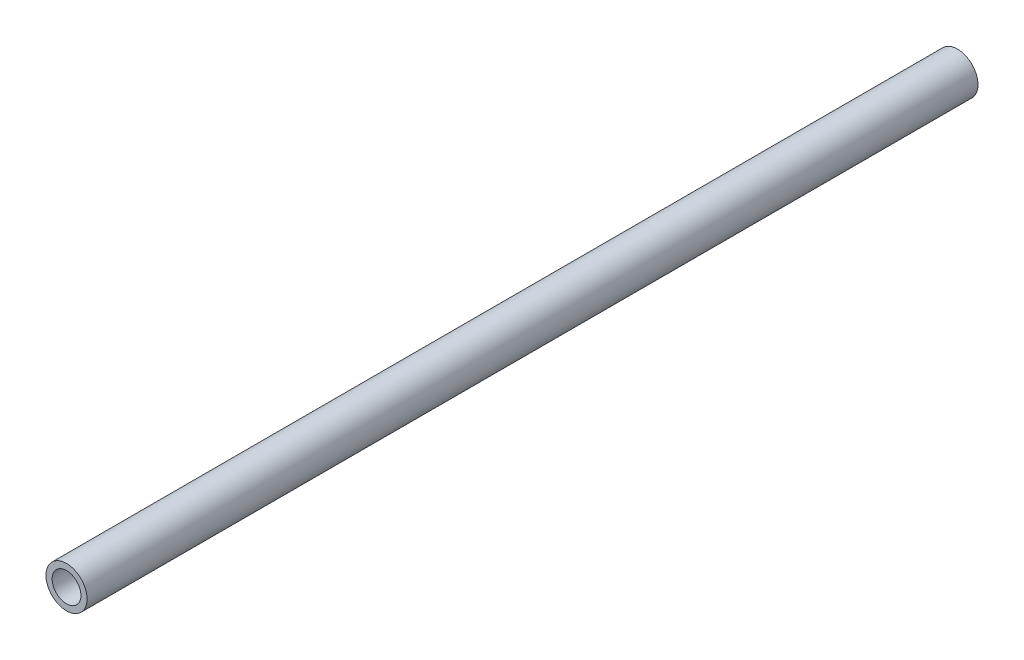
SolidWorks part; units mm, degrees
material "6063-T5"
ref_plane "Front Plane" through (0, 0, 0) normal (0, 0, 1) x (1, 0, 0)
ref_plane "Top Plane" through (0, 0, 0) normal (0, 1, 0) x (1, 0, 0)
ref_plane "Right Plane" through (0, 0, 0) normal (1, 0, 0) x (0, 0, -1)
sketch "Sketch1" plane through (0, 0, 0) normal (0, 0, 1) x (1, 0, 0)
  circle A0 centre (0, 0) radius 3.345
  circle A1 centre (0, 0) radius 2.345
  dimension "D1" = 6.69
  dimension "D2" = 1
extrude "Boss-Extrude1" add sketch "Sketch1" along normal blind 145
